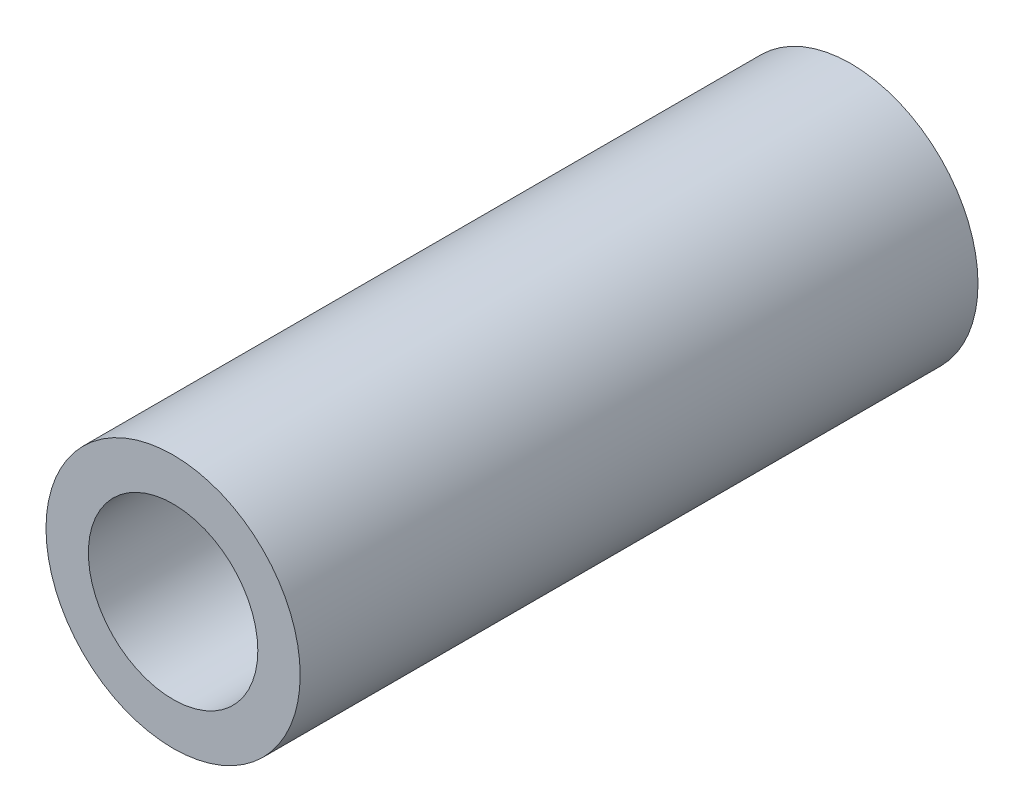
SolidWorks part; units mm, degrees
material "6061-T6 (SS)"
ref_plane "Front" through (0, 0, 0) normal (0, 0, 1) x (1, 0, 0)
ref_plane "Top" through (0, 0, 0) normal (0, 1, 0) x (1, 0, 0)
ref_plane "Right" through (0, 0, 0) normal (1, 0, 0) x (0, 0, -1)
sketch "Sketch1" plane through (0, 0, 0) normal (0, 0, 1) x (1, 0, 0)
  circle A0 centre (0, 0) radius 4.7625
  dimension "D1" = 9.525
extrude "Boss-Extrude1" add sketch "Sketch1" along normal mid plane 25.4
sketch "Sketch2" plane through (0, 0, 12.7) normal (0, 0, 1) x (1, 0, 0)
  circle A0 centre (0, 0) radius 3.175
  dimension "D1" = 6.35
extrude "Cut-Extrude1" cut sketch "Sketch2" against normal through all
